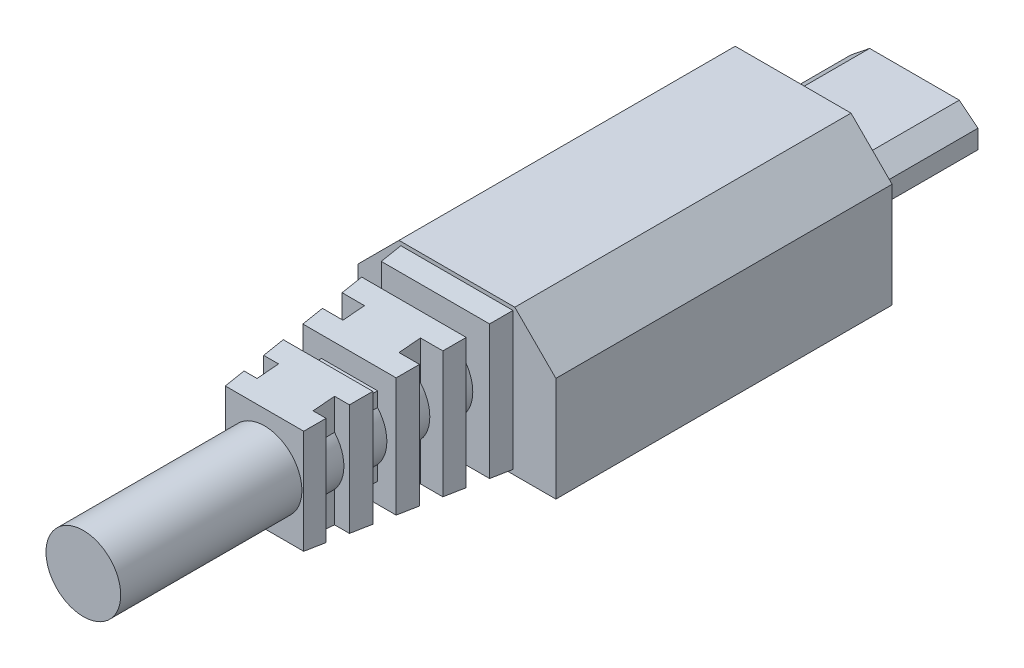
SolidWorks part; units mm, degrees
ref_plane "Front Plane" through (0, 0, 0) normal (0, 0, 1) x (1, 0, 0)
ref_plane "Top Plane" through (0, 0, 0) normal (0, 1, 0) x (1, 0, 0)
ref_plane "Right Plane" through (0, 0, 0) normal (1, 0, 0) x (0, 0, -1)
sketch "Sketch1" plane through (0, 0, 0) normal (0, 0, 1) x (1, 0, 0)
  line L0 (0, 1) -> (1, 1.8)
  line L1 (0, 0) -> (6.8, 0)
  line L2 (0, 0) -> (0, 1.8)
  line L3 (0, 1.8) -> (6.8, 1.8)
  line L4 (6.8, 0) -> (6.8, 1.8)
  line L5 (3.4, 1.8) -> (3.4, 0) construction
  line L6 (6.8, 1) -> (5.8, 1.8)
  line L8 (1.55, 0.2) -> (5.25, 0.2)
  line L9 (1.55, 0.2) -> (1.55, 0.85)
  line L10 (1.55, 0.85) -> (5.25, 0.85)
  line L11 (5.25, 0.2) -> (5.25, 0.85)
  point P15 (3.4, 0.85)
  dimension "D1" = 1.8
  dimension "D2" = 6.8
  dimension "D3" = 1
  dimension "D4" = 1
  dimension "D5" = 0.2
  dimension "D6" = 3.7
  dimension "D7" = 0.65
extrude "Boss-Extrude1" add sketch "Sketch1" along normal blind 6.5 contours L5 L3 L0 L2 L1 L8 L9 L10 | L3 L5 L10 L11 L8 L1 L4 L6
sketch "Sketch2" plane through (0, 0, 6.5) normal (0, 0, 1) x (1, 0, 0)
  line L0 (0, 0.7631) -> (-1.9, 0.7631) construction
  line L1 (-1.9, 4.8) -> (8.7, 4.8)
  line L2 (-1.9, 4.8) -> (-1.9, -3)
  line L3 (-1.9, -3) -> (8.7, -3)
  line L4 (8.7, 4.8) -> (8.7, -3)
  line L5 (-1.9, 2.6) -> (0.3, 4.8)
  line L6 (8.7, 2.6) -> (6.5, 4.8)
  line L7 (3.4, 4.8) -> (3.4, 1.8) construction
  line L8 (1, 1.8) -> (5.8, 1.8) construction
  line L9 (3.4, 0) -> (3.4, -3) construction
  line L10 (0, 0) -> (6.8, 0) construction
  line L13 (0, 0) -> (0, 1) construction
  line L14 (6.8, 0.7631) -> (8.7, 0.7631) construction
  line L15 (6.8, 0) -> (6.8, 1) construction
  line M1 (1.55, 0.85) -> (5.25, 0.85)
  line M2 (5.25, 0.85) -> (5.25, 0.2)
  line M3 (5.25, 0.2) -> (1.55, 0.2)
  line M4 (1.55, 0.2) -> (1.55, 0.85)
  line M5 (6.8, 1) -> (5.8, 1.8)
  line M6 (5.8, 1.8) -> (1, 1.8)
  line M7 (1, 1.8) -> (0, 1)
  line M8 (0, 1) -> (0, 0)
  line M9 (0, 0) -> (6.8, 0)
  line M10 (6.8, 0) -> (6.8, 1)
  dimension "D1" = 10.6
  dimension "D2" = 7.8
  dimension "D3" = 2.2
  dimension "D4" = 2.2
extrude "Boss-Extrude2" add sketch "Sketch2" along normal blind 18 contours L4 L6 L1 L5 L2 L3 M5 M10 M9 M8 M7 M6 | M10 M5 M6 M7 M8 M9 M4 M1 M2 M3 | M1 M4 M3 M2
sketch "Sketch5" plane through (0, 0, 24.5) normal (0, 0, 1) x (1, 0, 0)
  line L0 (0.3, 4.8) -> (6.5, 4.8) construction
  line L1 (6.4, 4.6) -> (0.4, 4.6)
  line L2 (6.4, 4.6) -> (6.4, -2.772)
  line L3 (6.4, -2.772) -> (0.4, -2.772)
  line L4 (0.4, 4.6) -> (0.4, -2.772)
  line L6 (3.4, 4.8) -> (3.4, 4.6) construction
  dimension "D1" = 0.2
  dimension "D2" = 6
extrude "Boss-Extrude4" add sketch "Sketch5" along normal blind 10.3 draft 5
sketch "Sketch7" plane through (0, 4.8, 0) normal (0, 1, 0) x (1, 0, 0)
  line L0 (3.4, -24.5) -> (3.4, -36.1996) construction
  line L1 (0.3, -24.5) -> (1.9, -24.5)
  line L2 (0.3, -24.5) -> (0.3, -25.65)
  line L3 (0.3, -25.65) -> (1.9, -25.65)
  line L4 (1.9, -24.5) -> (1.9, -25.65)
  line L5 (1.9, -25.65) -> (-0.2696, -25.65)
  line L6 (1.9, -25.65) -> (1.9, -26.8)
  line L7 (1.9, -26.8) -> (-0.2696, -26.8)
  line L8 (-0.2696, -25.65) -> (-0.2696, -26.8)
  line L9 (1.9, -26.8) -> (-0.2696, -26.8)
  line L10 (1.9, -26.8) -> (1.9, -27.95)
  line L11 (1.9, -27.95) -> (-0.2696, -27.95)
  line L12 (-0.2696, -26.8) -> (-0.2696, -27.95)
  line L13 (1.9, -27.95) -> (-0.2696, -27.95)
  line L14 (1.9, -27.95) -> (1.9, -29.1)
  line L15 (1.9, -29.1) -> (-0.2696, -29.1)
  line L16 (-0.2696, -27.95) -> (-0.2696, -29.1)
  line L17 (1.9, -29.1) -> (-0.2696, -29.1)
  line L18 (1.9, -29.1) -> (1.9, -30.25)
  line L19 (1.9, -30.25) -> (-0.2696, -30.25)
  line L20 (-0.2696, -29.1) -> (-0.2696, -30.25)
  line L21 (1.9, -30.25) -> (-0.2696, -30.25)
  line L22 (1.9, -30.25) -> (1.9, -31.4)
  line L23 (1.9, -31.4) -> (-0.2696, -31.4)
  line L24 (-0.2696, -30.25) -> (-0.2696, -31.4)
  line L25 (1.9, -31.4) -> (-0.2696, -31.4)
  line L26 (1.9, -31.4) -> (1.9, -32.55)
  line L27 (1.9, -32.55) -> (-0.2696, -32.55)
  line L28 (-0.2696, -31.4) -> (-0.2696, -32.55)
  line L29 (1.9, -32.55) -> (-0.2696, -32.55)
  line L30 (1.9, -32.55) -> (1.9, -33.7)
  line L31 (1.9, -33.7) -> (-0.2696, -33.7)
  line L32 (-0.2696, -32.55) -> (-0.2696, -33.7)
  line L33 (1.9, -33.7) -> (-0.2696, -33.7)
  line L34 (1.9, -33.7) -> (1.9, -34.85)
  line L35 (1.9, -34.85) -> (-0.2696, -34.85)
  line L36 (-0.2696, -33.7) -> (-0.2696, -34.85)
  line L37 (6.4, -24.5) -> (0.4, -24.5) construction
  line L38 (7.0696, -33.7) -> (7.0696, -34.85)
  line L39 (4.9, -34.85) -> (7.0696, -34.85)
  line L40 (4.9, -33.7) -> (4.9, -34.85)
  line L41 (4.9, -33.7) -> (7.0696, -33.7)
  line L42 (7.0696, -32.55) -> (7.0696, -33.7)
  line L43 (4.9, -33.7) -> (7.0696, -33.7)
  line L44 (4.9, -32.55) -> (4.9, -33.7)
  line L45 (4.9, -32.55) -> (7.0696, -32.55)
  line L46 (7.0696, -31.4) -> (7.0696, -32.55)
  line L47 (4.9, -32.55) -> (7.0696, -32.55)
  line L48 (4.9, -31.4) -> (4.9, -32.55)
  line L49 (4.9, -31.4) -> (7.0696, -31.4)
  line L50 (7.0696, -30.25) -> (7.0696, -31.4)
  line L51 (4.9, -31.4) -> (7.0696, -31.4)
  line L52 (4.9, -30.25) -> (4.9, -31.4)
  line L53 (4.9, -30.25) -> (7.0696, -30.25)
  line L54 (7.0696, -29.1) -> (7.0696, -30.25)
  line L55 (4.9, -30.25) -> (7.0696, -30.25)
  line L56 (4.9, -29.1) -> (4.9, -30.25)
  line L57 (4.9, -29.1) -> (7.0696, -29.1)
  line L58 (7.0696, -27.95) -> (7.0696, -29.1)
  line L59 (4.9, -29.1) -> (7.0696, -29.1)
  line L60 (4.9, -27.95) -> (4.9, -29.1)
  line L61 (4.9, -27.95) -> (7.0696, -27.95)
  line L62 (7.0696, -26.8) -> (7.0696, -27.95)
  line L63 (4.9, -27.95) -> (7.0696, -27.95)
  line L64 (4.9, -26.8) -> (4.9, -27.95)
  line L65 (4.9, -26.8) -> (7.0696, -26.8)
  line L66 (7.0696, -25.65) -> (7.0696, -26.8)
  line L67 (4.9, -26.8) -> (7.0696, -26.8)
  line L68 (4.9, -25.65) -> (4.9, -26.8)
  line L69 (4.9, -25.65) -> (7.0696, -25.65)
  line L70 (4.9, -24.5) -> (4.9, -25.65)
  line L71 (6.5, -25.65) -> (4.9, -25.65)
  line L72 (6.5, -24.5) -> (6.5, -25.65)
  line L73 (6.5, -24.5) -> (4.9, -24.5)
  dimension "D1" = 1.15
  dimension "D2" = 1.6
extrude "Cut-Extrude1" cut sketch "Sketch7" against normal blind 10.3 contours L5 L8 L7 L6 L3 | L11 L16 L15 L14 | L19 L24 L23 L22 | L27 L32 L31 L30 | L69 L68 L65 L66 | L61 L60 L57 L58 | L53 L52 L49 L50 | L45 L44 L41 L42
sketch "Sketch9" plane through (8.7, 0, 0) normal (1, 0, 0) x (0, 0, -1)
  line L0 (-36.8785, 0.9) -> (-25.1788, 0.9) construction
  line L1 (-34.85, -2.8) -> (-34.85, -1.2)
  line L2 (-34.85, -2.8) -> (-33.7, -2.8)
  line L3 (-33.7, -2.8) -> (-33.7, -1.2)
  line L4 (-34.85, -1.2) -> (-33.7, -1.2)
  line L5 (-33.7, -1.2) -> (-33.7, -2.8)
  line L6 (-33.7, -1.2) -> (-32.55, -1.2)
  line L7 (-32.55, -1.2) -> (-32.55, -2.8)
  line L8 (-33.7, -2.8) -> (-32.55, -2.8)
  line L9 (-32.55, -1.2) -> (-32.55, -2.8)
  line L10 (-32.55, -1.2) -> (-31.4, -1.2)
  line L11 (-31.4, -1.2) -> (-31.4, -2.8)
  line L12 (-32.55, -2.8) -> (-31.4, -2.8)
  line L13 (-31.4, -1.2) -> (-31.4, -2.8)
  line L14 (-31.4, -1.2) -> (-30.25, -1.2)
  line L15 (-30.25, -1.2) -> (-30.25, -2.8)
  line L16 (-31.4, -2.8) -> (-30.25, -2.8)
  line L17 (-30.25, -1.2) -> (-30.25, -2.8)
  line L18 (-30.25, -1.2) -> (-29.1, -1.2)
  line L19 (-29.1, -1.2) -> (-29.1, -2.8)
  line L20 (-30.25, -2.8) -> (-29.1, -2.8)
  line L21 (-29.1, -1.2) -> (-29.1, -2.8)
  line L22 (-29.1, -1.2) -> (-27.95, -1.2)
  line L23 (-27.95, -1.2) -> (-27.95, -2.8)
  line L24 (-29.1, -2.8) -> (-27.95, -2.8)
  line L25 (-27.95, -1.2) -> (-27.95, -2.8)
  line L26 (-27.95, -1.2) -> (-26.8, -1.2)
  line L27 (-26.8, -1.2) -> (-26.8, -2.8)
  line L28 (-27.95, -2.8) -> (-26.8, -2.8)
  line L29 (-26.8, -1.2) -> (-26.8, -2.8)
  line L30 (-26.8, -1.2) -> (-25.65, -1.2)
  line L31 (-25.65, -1.2) -> (-25.65, -2.8)
  line L32 (-26.8, -2.8) -> (-25.65, -2.8)
  line L33 (-25.65, -1.2) -> (-25.65, -2.8)
  line L34 (-25.65, -1.2) -> (-24.5, -1.2)
  line L35 (-24.5, -1.2) -> (-24.5, -2.8)
  line L36 (-25.65, -2.8) -> (-24.5, -2.8)
  line L37 (-25.65, 4.6) -> (-24.5, 4.6)
  line L38 (-24.5, 3) -> (-24.5, 4.6)
  line L39 (-25.65, 3) -> (-24.5, 3)
  line L40 (-25.65, 3) -> (-25.65, 4.6)
  line L41 (-26.8, 4.6) -> (-25.65, 4.6)
  line L42 (-25.65, 3) -> (-25.65, 4.6)
  line L43 (-26.8, 3) -> (-25.65, 3)
  line L44 (-26.8, 3) -> (-26.8, 4.6)
  line L45 (-27.95, 4.6) -> (-26.8, 4.6)
  line L46 (-26.8, 3) -> (-26.8, 4.6)
  line L47 (-27.95, 3) -> (-26.8, 3)
  line L48 (-27.95, 3) -> (-27.95, 4.6)
  line L49 (-29.1, 4.6) -> (-27.95, 4.6)
  line L50 (-27.95, 3) -> (-27.95, 4.6)
  line L51 (-29.1, 3) -> (-27.95, 3)
  line L52 (-29.1, 3) -> (-29.1, 4.6)
  line L53 (-30.25, 4.6) -> (-29.1, 4.6)
  line L54 (-29.1, 3) -> (-29.1, 4.6)
  line L55 (-30.25, 3) -> (-29.1, 3)
  line L56 (-30.25, 3) -> (-30.25, 4.6)
  line L57 (-31.4, 4.6) -> (-30.25, 4.6)
  line L58 (-30.25, 3) -> (-30.25, 4.6)
  line L59 (-31.4, 3) -> (-30.25, 3)
  line L60 (-31.4, 3) -> (-31.4, 4.6)
  line L61 (-32.55, 4.6) -> (-31.4, 4.6)
  line L62 (-31.4, 3) -> (-31.4, 4.6)
  line L63 (-32.55, 3) -> (-31.4, 3)
  line L64 (-32.55, 3) -> (-32.55, 4.6)
  line L65 (-33.7, 4.6) -> (-32.55, 4.6)
  line L66 (-32.55, 3) -> (-32.55, 4.6)
  line L67 (-33.7, 3) -> (-32.55, 3)
  line L68 (-33.7, 3) -> (-33.7, 4.6)
  line L69 (-34.85, 3) -> (-33.7, 3)
  line L70 (-33.7, 4.6) -> (-33.7, 3)
  line L71 (-34.85, 4.6) -> (-33.7, 4.6)
  line L72 (-34.85, 4.6) -> (-34.85, 3)
  dimension "D1" = 1.15
  dimension "D2" = 1.6
  dimension "D3" = 2.1
extrude "Cut-Extrude2" cut sketch "Sketch9" against normal blind 10.3 contours L44 L43 L40 L41 | L60 L59 L56 L57 | L27 L32 L31 L30 | L11 L16 L15 L14
sketch "Sketch3" plane through (0, 0, 24.5) normal (0, 0, 1) x (1, 0, 0)
  line L0 (3.4, 4.8) -> (3.4, 0.9) construction
  line L1 (0.3, 4.8) -> (6.5, 4.8) construction
  line L2 (3.4, 0.9) -> (-1.9, 0.9) construction
  line L3 (-1.9, 2.6) -> (-1.9, -3) construction
  line L4 (3.4, 0.9) -> (3.4, -3) construction
  line L5 (-1.9, -3) -> (8.7, -3) construction
  line L6 (3.4, 0.9) -> (8.7, 0.9) construction
  line L7 (8.7, 2.6) -> (8.7, -3) construction
  line L8 (8.7, 4.8) -> (8.7, -3) construction
  circle A0 centre (3.4, 0.9) radius 2
extrude "Boss-Extrude3" add sketch "Sketch3" along normal blind 20
